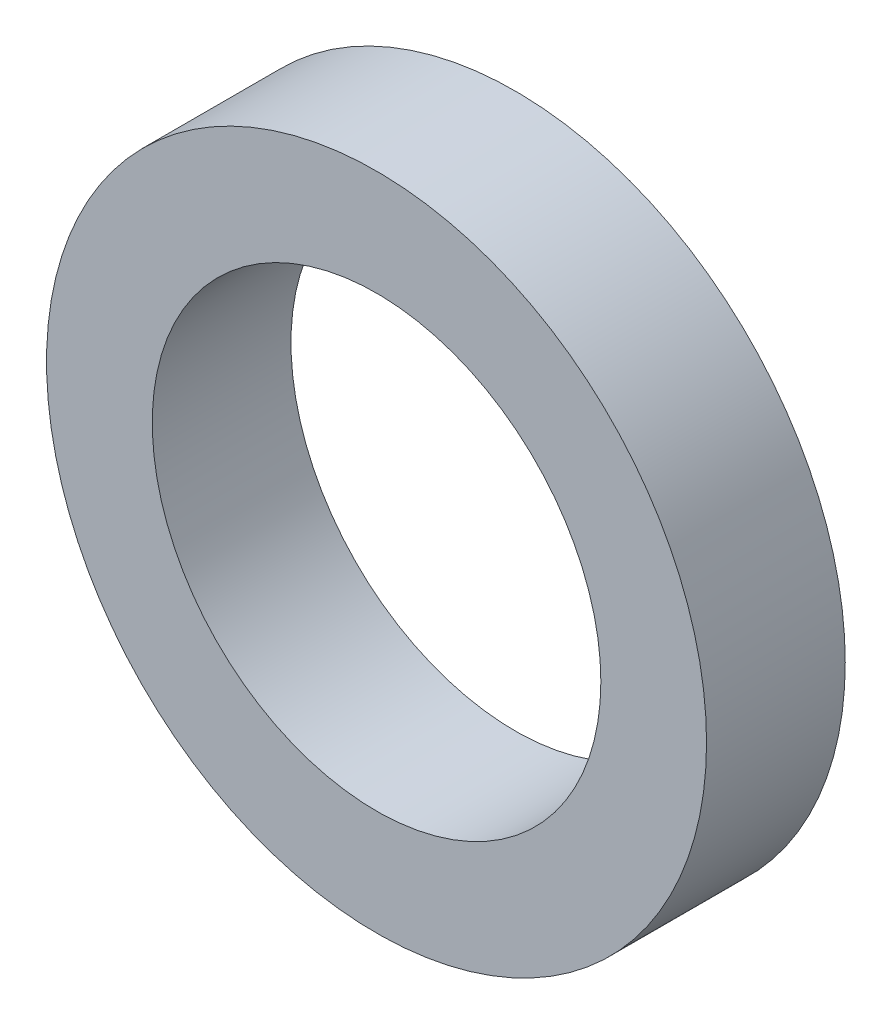
SolidWorks part; units mm, degrees
material "Boron"
ref_plane "Front" through (0, 0, 0) normal (0, 0, 1) x (1, 0, 0)
ref_plane "Top" through (0, 0, 0) normal (0, 1, 0) x (1, 0, 0)
ref_plane "Right" through (0, 0, 0) normal (1, 0, 0) x (0, 0, -1)
sketch "Sketch1" plane through (0, 0, 0) normal (0, 0, 1) x (1, 0, 0)
  circle A0 centre (0, 0) radius 128
  circle A1 centre (0, 0) radius 87
extrude "Boss-Extrude2" add sketch "Sketch1" along normal blind 53.8 separate body contours A0 | A1
